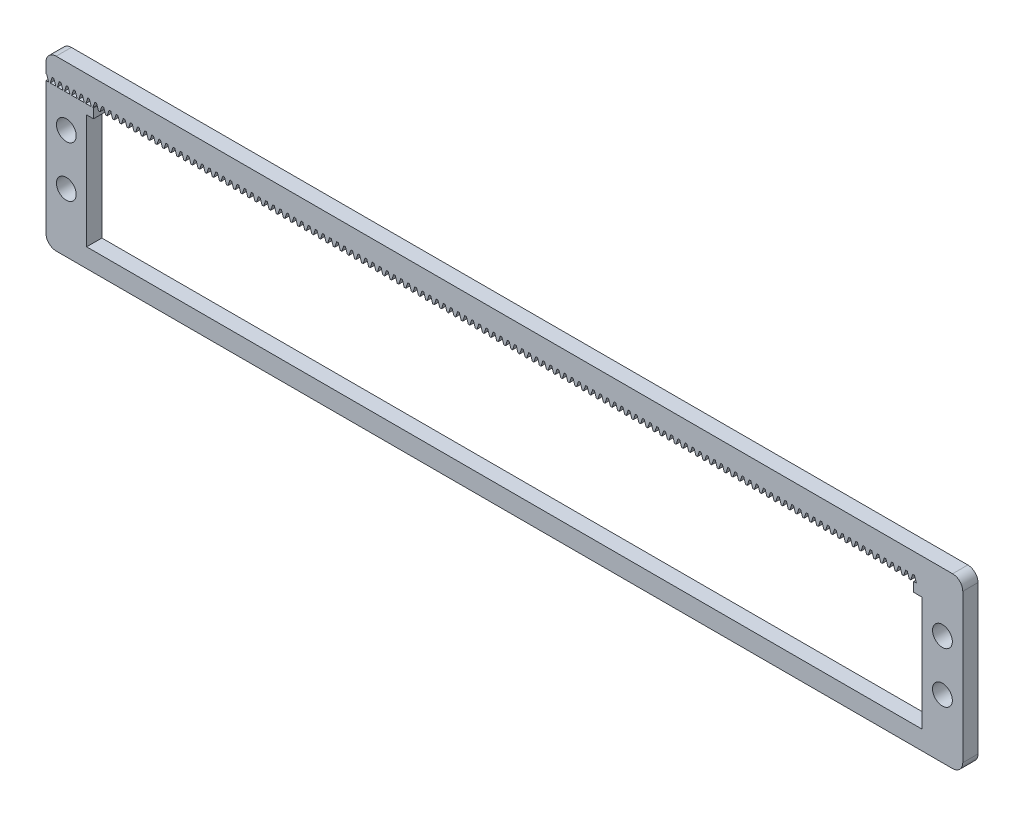
SolidWorks part; units mm, degrees
other "Markup1"
sketch "Sketch6" plane through (0, -30, 3.6) normal (0, 0, 1) x (1, 0, 0)
other "Markup2"
sketch "Sketch7" plane through (0, -30, 3.6) normal (0, 0, 1) x (1, 0, 0)
ref_plane "Front Plane" through (0, 0, 0) normal (0, 0, 1) x (1, 0, 0)
ref_plane "Top Plane" through (0, 0, 0) normal (0, 1, 0) x (1, 0, 0)
ref_plane "Right Plane" through (0, 0, 0) normal (1, 0, 0) x (0, 0, -1)
sketch "Sketch1" plane through (0, 0, 0) normal (0, 0, 1) x (1, 0, 0)
  line L1 (2, 0) -> (178.46, 0)
  line L2 (0, -2) -> (0, -31.22)
  line L3 (2, -33.22) -> (178.46, -33.22)
  line L4 (180.46, -2) -> (180.46, -31.22)
  arc A0 (178.46, -33.22) -> (180.46, -31.22) centre (178.46, -31.22) ccw
  arc A1 (0, -31.22) -> (2, -33.22) centre (2, -31.22) ccw
  arc A2 (2, 0) -> (0, -2) centre (2, -2) ccw
  arc A3 (178.46, 0) -> (180.46, -2) centre (178.46, -2) cw
  point P7 (180.46, -33.22)
  point P12 (0, 0)
  point P15 (180.46, 0)
  dimension "D3" = 2
  dimension "D1" = 33.22
  dimension "D2" = 180.46
extrude "Boss-Extrude1" add sketch "Sketch1" along normal blind 3
sketch "Sketch2" plane through (0, 0, 3) normal (0, 0, 1) x (1, 0, 0)
  line L0 (2, -33.22) -> (178.46, -33.22) construction
  line L1 (8, -7) -> (172.46, -7)
  line L2 (8, -7) -> (8, -29.5)
  line L3 (8, -29.5) -> (172.46, -29.5)
  line L4 (172.46, -7) -> (172.46, -29.5)
  line L5 (0, -2) -> (0, -31.22) construction
  line L7 (180.46, -31.22) -> (180.46, -2) construction
  line L8 (8, -18.25) -> (172.46, -18.25) construction
  line L12 (8, -29.5) -> (172.46, -29.5) construction
  line L13 (172.46, -4.3144) -> (172.46, -29.5) construction
  dimension "D1" = 22.5
  dimension "D2" = 8
  dimension "D3" = 8
  dimension "D4" = 3.72
extrude "Cut-Extrude1" cut sketch "Sketch2" against normal through all
sketch "Sketch3" plane through (0, 0, 3) normal (0, 0, 1) x (1, 0, 0)
  line L0 (172.46, -7) -> (8, -7) construction
  line L1 (9.35, -7) -> (170.78, -7)
  line L2 (9.35, -7) -> (9.35, -5.15)
  line L3 (9.35, -5.15) -> (170.78, -5.15)
  line L4 (170.78, -7) -> (170.78, -5.15)
  line L5 (172.46, -29.5) -> (172.46, -7) construction
  line L6 (8, -7) -> (8, -29.5) construction
  dimension "D1" = 1.85
  dimension "D2" = 1.68
  dimension "D3" = 1.35
extrude "Cut-Extrude2" cut sketch "Sketch3" against normal through all
sketch "Sketch4" plane through (0, 0, 3) normal (0, 0, 1) x (1, 0, 0)
  line L0 (171.805, -5.15) -> (171.325, -5.15) construction
  line L1 (170.78, -5.15) -> (9.35, -5.15) construction
  line L2 (171.805, -5.15) -> (172.185, -4.0118) construction
  line L3 (172.185, -4.0118) -> (170.945, -4.0118) construction
  line L4 (170.945, -4.0118) -> (171.325, -5.15)
  line L5 (170.945, -4.0118) -> (170.615, -4.0118)
  line L6 (170.615, -4.0118) -> (170.235, -5.15)
  line L7 (170.235, -5.15) -> (171.325, -5.15)
  line L10 (171.325, -5.15) -> (171.805, -5.15) construction
  dimension "D1" = 0.48
  dimension "D2" = 1.2
  dimension "D3" = 1.2
  dimension "D4" = 0.33
  dimension "D5" = 1.24
  dimension "D6" = 1.2
extrude "Cut-Extrude4" cut sketch "Sketch4" against normal through all
pattern_linear "LPattern1" count 141 spacing 1.4 along (-1, 0, 0) of "Cut-Extrude4"
sketch "Sketch5" plane through (0, 0, 3) normal (0, 0, 1) x (1, 0, 0)
  line L0 (172.46, -16.61) -> (180.46, -16.61) construction
  line L1 (178.46, 0) -> (2, 0) construction
  line L2 (8, -7) -> (8, -29.5) construction
  line L3 (0, -2) -> (0, -4.0118) construction
  line L4 (2, -33.22) -> (178.46, -33.22) construction
  line L5 (0, -16.61) -> (8, -16.61) construction
  line L7 (176.46, -11.61) -> (176.46, -21.61) construction
  line L8 (4, -11.61) -> (4, -21.61) construction
  line L9 (172.46, -29.5) -> (172.46, -7) construction
  line L10 (180.46, -31.22) -> (180.46, -2) construction
  circle A4 centre (4, -11.61) radius 1.95
  circle A5 centre (4, -21.61) radius 1.95
  circle A6 centre (176.46, -11.61) radius 1.95
  circle A7 centre (176.46, -21.61) radius 1.95
  point P8 (176.46, -16.61)
  point P18 (4, -16.61)
  point P22 (4, -16.61)
  point P31 (176.46, -16.61)
  dimension "D1" = 3.9
  dimension "D3" = 3.9
  dimension "D4" = 3.9
  dimension "D6" = 3.9
  dimension "D5" = 10
  dimension "D7" = 10
extrude "Cut-Extrude5" cut sketch "Sketch5" against normal blind 10
